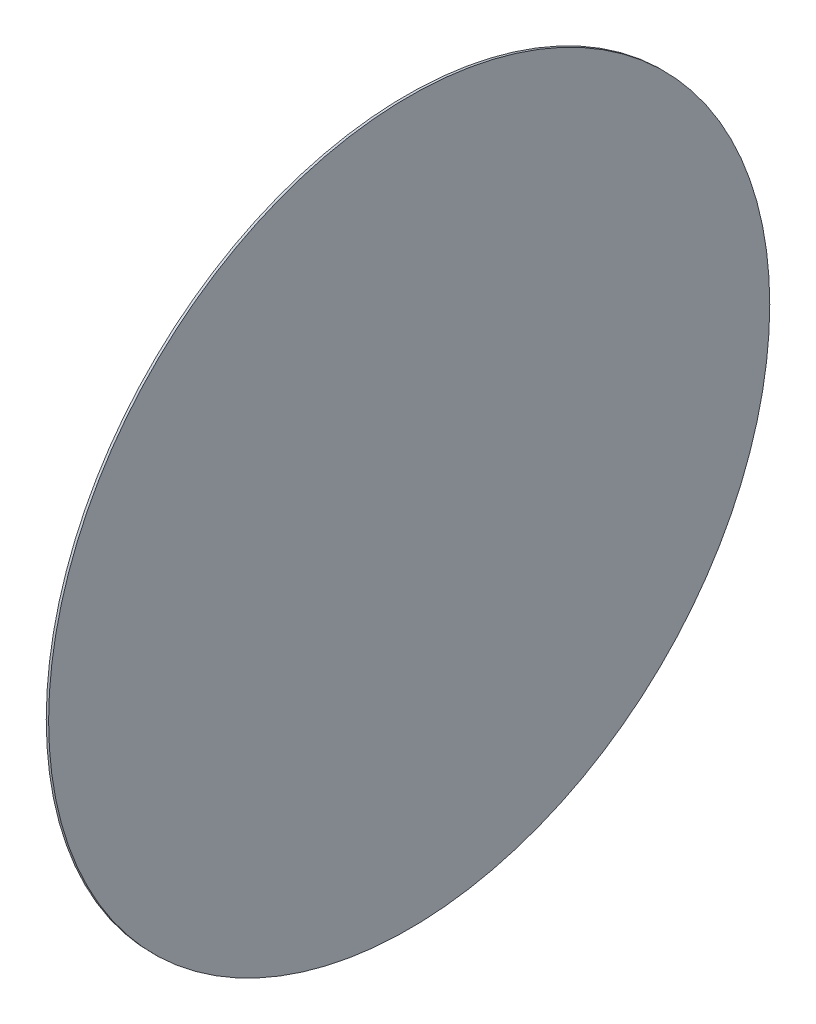
SolidWorks part; units mm, degrees
ref_plane "前视基准面" through (0, 0, 0) normal (0, 0, 1) x (1, 0, 0)
ref_plane "上视基准面" through (0, 0, 0) normal (0, 1, 0) x (1, 0, 0)
ref_plane "右视基准面" through (0, 0, 0) normal (1, 0, 0) x (0, 0, -1)
sketch "草图1" plane through (0, 0, 0) normal (0, 0, 1) x (1, 0, 0)
  line L0 (0, 9) -> (0, 0)
  line L2 (0, 9) -> (0.059, 9)
  line L3 (0, 0) -> (0.059, 0)
  line L4 (0.059, 9) -> (0.059, 0)
  dimension "D1" = 9
  dimension "D2" = 0.059
revolve "旋转2" add sketch "草图1" angle 360 about L3
